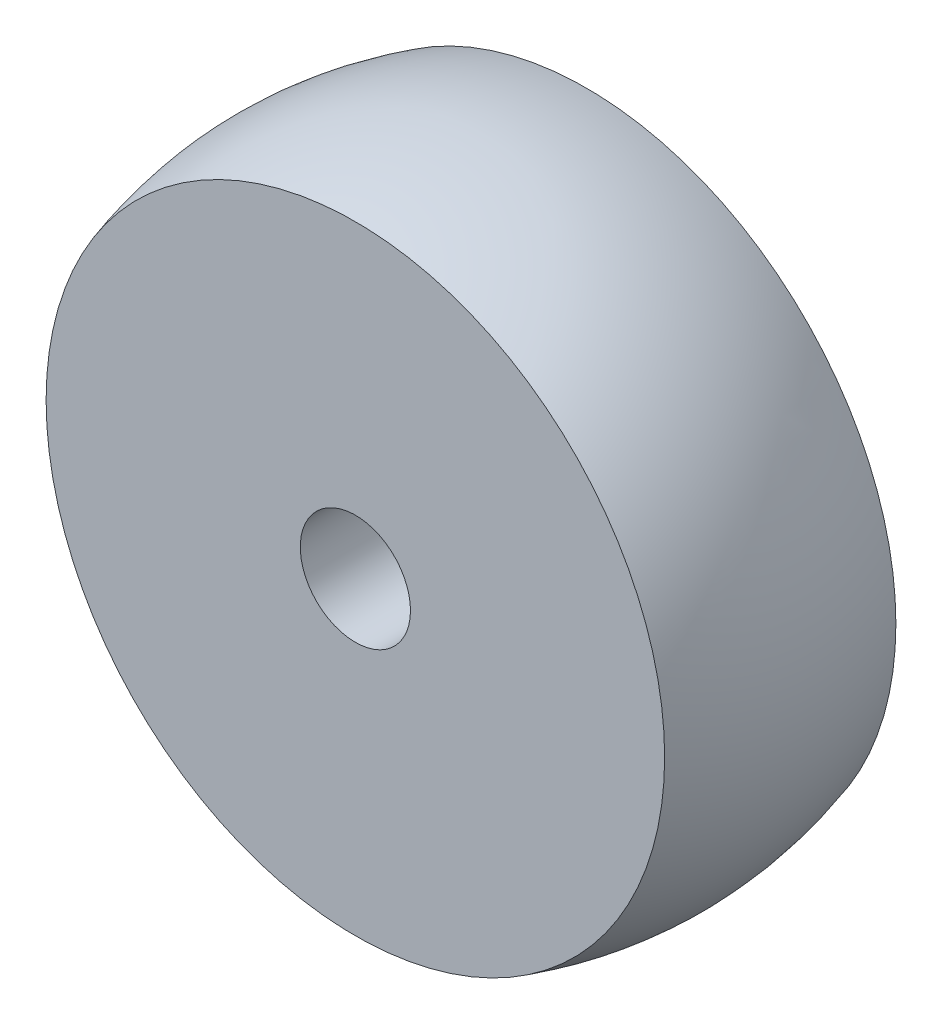
SolidWorks part; units mm, degrees
ref_plane "Front Plane" through (0, 0, 0) normal (0, 0, 1) x (1, 0, 0)
ref_plane "Top Plane" through (0, 0, 0) normal (0, 1, 0) x (1, 0, 0)
ref_plane "Right Plane" through (0, 0, 0) normal (1, 0, 0) x (0, 0, -1)
sketch "Sketch1" plane through (0, 0, 0) normal (0, 0, 1) x (1, 0, 0)
  circle A0 centre (0, 0) radius 26.75
  circle A1 centre (0, 0) radius 4.765
  dimension "D1" = 53.5
  dimension "D2" = 9.53
extrude "Boss-Extrude1" add sketch "Sketch1" along normal blind 20
sketch "Sketch2" plane through (0, 0, 0) normal (1, 0, 0) x (0, 0, -1)
  line L1 (0, 0) -> (-17.8426, 0) construction
  line L2 (-20, 26.75) -> (0, 26.75)
  spline S0 degree 2 poles (-20, 26.75) (-10, 29.75) (0, 26.75) knots 0 0 0 1 1 1
  dimension "D1" = 1.5
revolve "Revolve1" add sketch "Sketch2" angle 360 about L1
